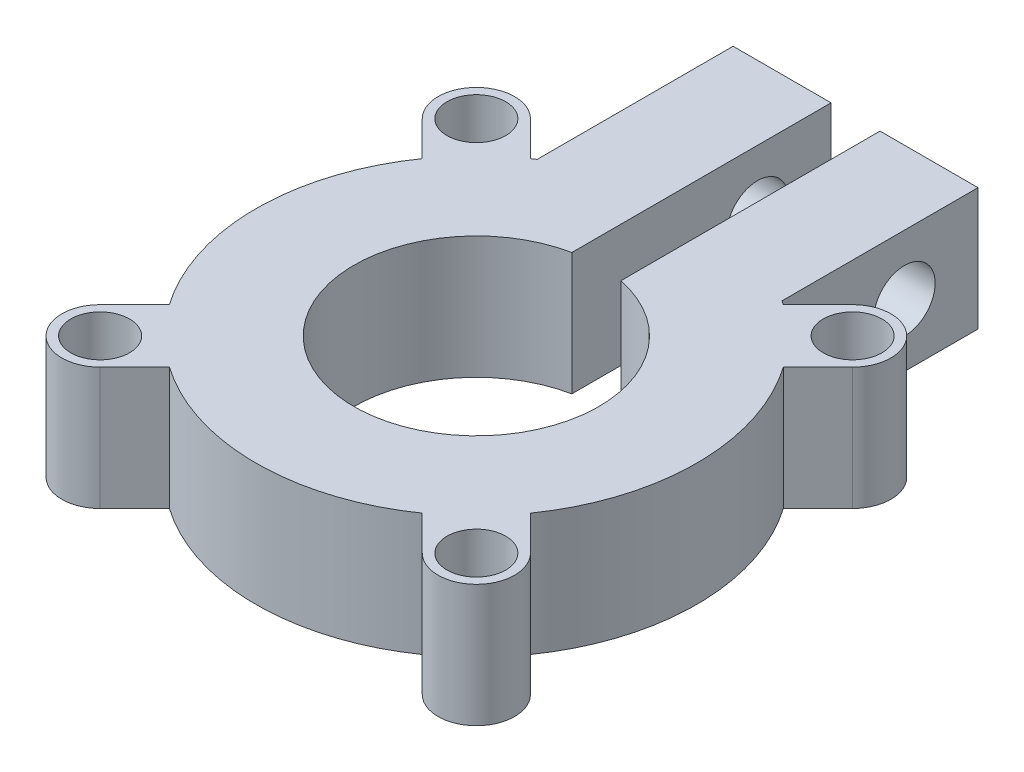
SolidWorks part; units mm, degrees
ref_plane "Front Plane" through (0, 0, 0) normal (0, 0, 1) x (1, 0, 0)
ref_plane "Top Plane" through (0, 0, 0) normal (0, 1, 0) x (1, 0, 0)
ref_plane "Right Plane" through (0, 0, 0) normal (1, 0, 0) x (0, 0, -1)
sketch "Sketch1" plane through (0, 0, 0) normal (0, 1, 0) x (1, 0, 0)
  line L3 (3.175, 4.7519) -> (3.175, 9.8319)
  line L4 (3.175, 9.8319) -> (-3.175, 9.8319)
  line L5 (-3.175, 4.7519) -> (-3.175, 9.8319)
  circle A0 centre (0, 0) radius 3.175
  arc A1 (-3.175, 4.7519) -> (3.175, 4.7519) centre (0, 0) ccw
  point P3 (0, 9.8319)
  dimension "D1" = 6.35
  dimension "D2" = 2.54
  dimension "D3" = 6.35
  dimension "D4" = 5.08
extrude "Boss-Extrude1" add sketch "Sketch1" along normal blind 3.175
sketch "Sketch3" plane through (0, 3.175, 0) normal (0, 1, 0) x (1, 0, 0)
  line L0 (3.175, 9.8319) -> (-3.175, 9.8319) construction
  line L1 (-0.635, 9.8319) -> (0.635, 9.8319)
  line L2 (-0.635, 9.8319) -> (-0.635, 3.1109)
  line L3 (-0.635, 3.1109) -> (0.635, 3.1109)
  line L4 (0.635, 9.8319) -> (0.635, 3.1109)
  circle A0 centre (0, 0) radius 3.175 construction
  point P4 (0, 3.1109)
  point P6 (0, 0)
  point P9 (0, 0)
  dimension "D1" = 1.27
extrude "Cut-Extrude1" cut sketch "Sketch3" against normal blind 3.175
sketch "Sketch4" plane through (3.175, 0, 0) normal (1, 0, 0) x (0, 0, -1)
  line L0 (8.895, 3.175) -> (8.895, 0) construction
  line L1 (4.7519, 3.175) -> (9.8319, 3.175) construction
  line L2 (4.7519, 0) -> (9.8319, 0) construction
  line L3 (4.7519, 1.5875) -> (9.8319, 1.5875) construction
  line L4 (4.7519, 3.175) -> (4.7519, 0) construction
  line L5 (9.8319, 3.175) -> (9.8319, 0) construction
  circle A0 centre (7.9269, 1.5875) radius 0.7938
  point P8 (8.895, 1.5875)
  dimension "D1" = 1.5875
  dimension "D2" = 1.905
extrude "Cut-Extrude2" cut sketch "Sketch4" against normal through all
sketch "Sketch5" plane through (0, 0, 0) normal (0, -1, 0) x (1, 0, 0)
  line L0 (6.7629, 6.7629) -> (-6.7629, -6.7629) construction
  line L1 (6.7629, -6.7629) -> (-6.7629, 6.7629) construction
  line L2 (0, 0) -> (0, 2.501) construction
  line L3 (-3.2782, -4.6813) -> (-4.1762, -5.5794)
  line L4 (-4.6813, -3.2782) -> (-5.5794, -4.1762)
  line L5 (-5.5794, -4.1762) -> (-4.1762, -5.5794) construction
  arc A0 (3.175, -4.7519) -> (-3.175, -4.7519) centre (0, 0) ccw construction
  arc A1 (-5.5794, -4.1762) -> (-4.1762, -5.5794) centre (-4.8778, -4.8778) ccw
  circle A2 centre (-4.8778, -4.8778) radius 0.762
  point P5 (0, 0)
  point P6 (0, 0)
  point P19 (-4.8778, -4.8778)
  point P20 (-7.7115, -7.7115)
  point P23 (0, 0)
  arc M10 (3.175, -4.7519) -> (-3.175, -4.7519) centre (0, 0) ccw
  dimension "D4" = 1.524
  dimension "D1" = 45
  dimension "D2" = 1.9844
  dimension "D3" = 1.27
extrude "Boss-Extrude2" add sketch "Sketch5" against normal blind 3.175 contours L4 A1 L3 A2 M10
mirror "Mirror1" about plane through (0, 0, 0) normal (1, 0, 0) of "Boss-Extrude2" second plane through (0, 0, 0) second plane normal (0, 0, 1)
